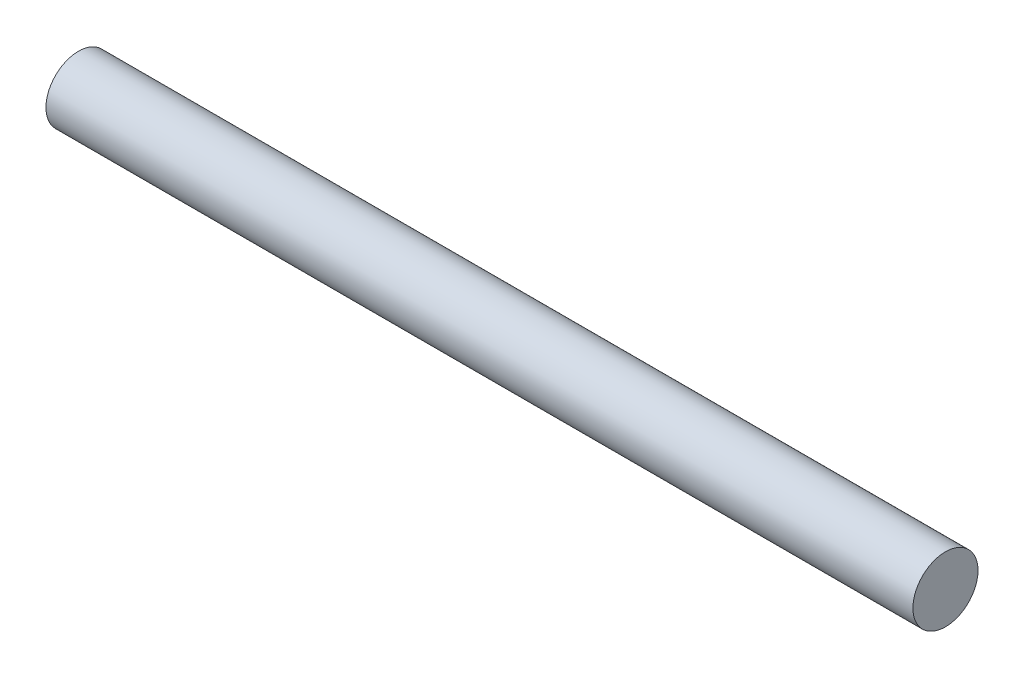
SolidWorks part; units mm, degrees
ref_plane "Front Plane" through (0, 0, 0) normal (0, 0, 1) x (1, 0, 0)
ref_plane "Top Plane" through (0, 0, 0) normal (0, 1, 0) x (1, 0, 0)
ref_plane "Right Plane" through (0, 0, 0) normal (1, 0, 0) x (0, 0, -1)
sketch "Sketch1" plane through (0, 0, 0) normal (1, 0, 0) x (0, 0, -1)
  circle A0 centre (0, 0) radius 6.35
  dimension "D1" = 12.7
extrude "Boss-Extrude1" add sketch "Sketch1" along normal blind 169.164
